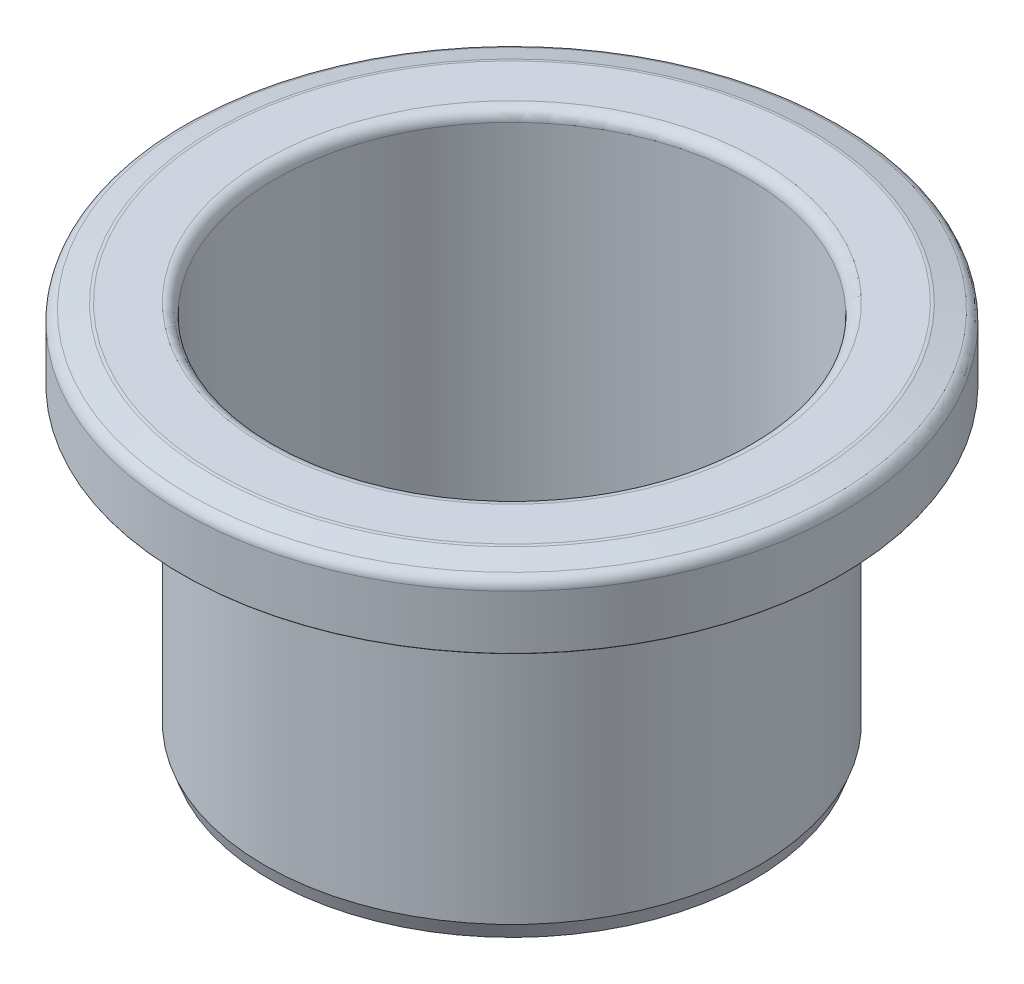
SolidWorks part; units mm, degrees
ref_plane "Piano frontale" through (0, 0, 0) normal (0, 0, 1) x (1, 0, 0)
ref_plane "Piano superiore" through (0, 0, 0) normal (0, 1, 0) x (1, 0, 0)
ref_plane "Piano destro" through (0, 0, 0) normal (1, 0, 0) x (0, 0, -1)
sketch "Schizzo1" plane through (0, 0, 0) normal (0, 0, 1) x (1, 0, 0)
  line L9 (0, -2) -> (22, -2) construction
  line L10 (22, -2) -> (22, 32)
  line L11 (0, -2) -> (0, 30) construction
  line L12 (22, 32) -> (27, 32)
  line L13 (29.5, 31.3301) -> (29.5, 26)
  line L14 (27, 32) -> (29.5, 31.3301)
  point P5 (0, 0)
  dimension "D1" = 22
  dimension "D2" = 5
  dimension "D3" = 6
  dimension "D4" = 5.3301
  dimension "D5" = 15
  dimension "D6" = 34
surface "Superficie-Rivoluzione2" sketch "Schizzo1" parameters "D1"=360
thicken "Spessore1" thickness 0.5 thickness side both sides parameters "D1"=0.5
fillet "Raccordo1" radius 0.05 3 edges at (0, 26, 29) (0, 26, 30) (0, -2, 21.5)
fillet "Raccordo2" radius 1 6 edges at (0, 32.5, 21.5) (0, 32.5, 27.0658) (0, 31.7138, -30) (0, 31.5, 26.9342) (0, 30.9465, -29) (0, 31.5, 22.5)
chamfer "Smusso1" distance 0.5 angle 70 1 edges at (0, -2, 22.5)
